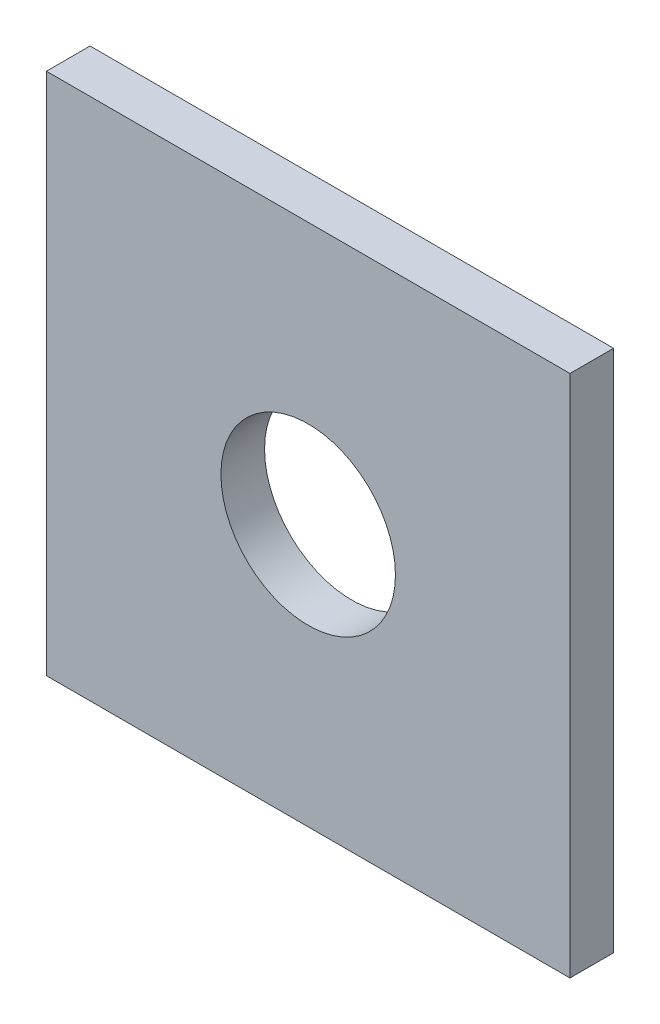
SolidWorks part; units mm, degrees
material "Plain Carbon Steel"
ref_plane "Front Plane" through (0, 0, 0) normal (0, 0, 1) x (1, 0, 0)
ref_plane "Top Plane" through (0, 0, 0) normal (0, 1, 0) x (1, 0, 0)
ref_plane "Right Plane" through (0, 0, 0) normal (1, 0, 0) x (0, 0, -1)
sketch "Sketch1" plane through (0, 0, 0) normal (0, 0, 1) x (1, 0, 0)
  line L1 (0, 0) -> (76.2, 0)
  line L2 (0, 0) -> (0, 76.2)
  line L3 (0, 76.2) -> (76.2, 76.2)
  line L4 (76.2, 0) -> (76.2, 76.2)
  circle A0 centre (38.1, 38.1) radius 12.7
  dimension "D3" = 25.4
  dimension "D1" = 76.2
  dimension "D2" = 76.2
  dimension "D4" = 38.1
  dimension "D5" = 38.1
extrude "Boss-Extrude1" add sketch "Sketch1" along normal blind 6.35
